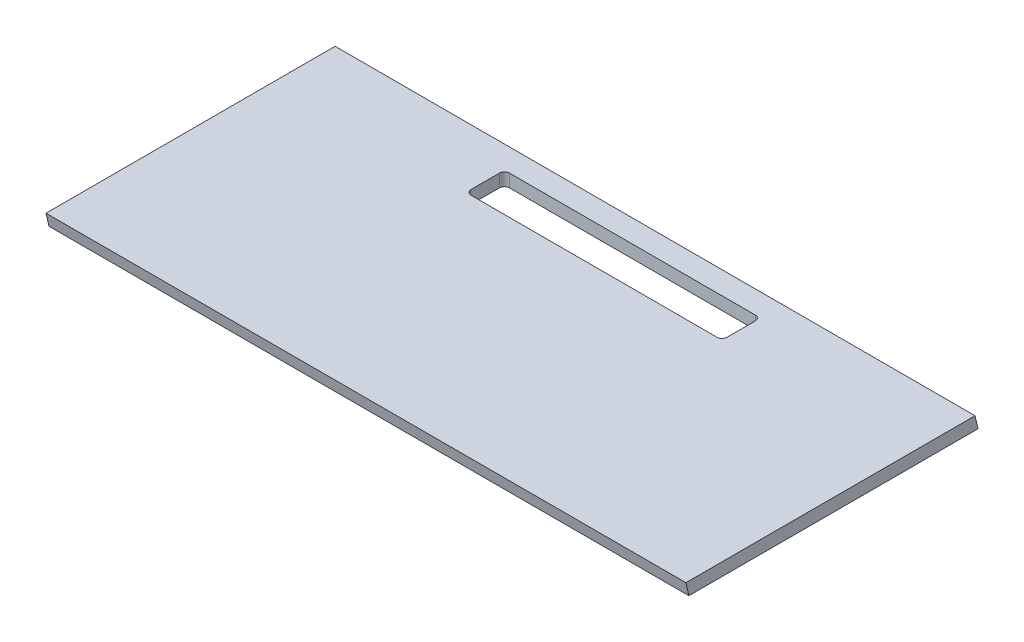
SolidWorks part; units mm, degrees
ref_plane "Ön Düzlem" through (0, 0, 0) normal (0, 0, 1) x (1, 0, 0)
ref_plane "Üst Düzlem" through (0, 0, 0) normal (0, 1, 0) x (1, 0, 0)
ref_plane "Sağ Düzlem" through (0, 0, 0) normal (1, 0, 0) x (0, 0, -1)
sketch "Sketch2" plane through (0, 0, 0) normal (0, 1, 0) x (1, 0, 0)
  line L1 (-250, -114.1) -> (250, -114.1)
  line L2 (-250, -114.1) -> (-250, 114.1)
  line L3 (-250, 114.1) -> (250, 114.1)
  line L4 (250, -114.1) -> (250, 114.1)
  line L5 (-250, -114.1) -> (250, 114.1) construction
  line L6 (-250, 114.1) -> (250, -114.1) construction
  point P0 (0, 0)
  dimension "D1" = 500
  dimension "D2" = 228.2
extrude "Boss-Extrude1" add sketch "Sketch2" along normal blind 10
sketch "Sketch3" plane through (0, 10, 0) normal (0, 1, 0) x (1, 0, 0)
  line L1 (-100, 94.1) -> (100, 94.1)
  line L2 (-100, 94.1) -> (-100, 64.1)
  line L3 (-100, 64.1) -> (100, 64.1)
  line L4 (100, 94.1) -> (100, 64.1)
  line L5 (-100, 94.1) -> (100, 64.1) construction
  line L6 (-100, 64.1) -> (100, 94.1) construction
  line L7 (250, 114.1) -> (-250, 114.1) construction
  point P0 (0, 0)
  dimension "D1" = 200
  dimension "D2" = 30
  dimension "D3" = 20
extrude "Cut-Extrude1" cut sketch "Sketch3" along direction (0, -1, 0) on the side against the normal up to next (10 mm away)
fillet "Fillet1" radius 4 4 edges at (100, 5, -94.1) (100, 5, -64.1) (-100, 5, -64.1) (-100, 5, -94.1)
sketch "Sketch4" plane through (250, 0, 0) normal (1, 0, 0) x (0, 0, -1)
  line L0 (114.1, 0) -> (111.7913, 10)
  line L1 (-114.1, 10) -> (114.1, 10) construction
  line L2 (111.7913, 10) -> (114.1, 10)
  line L3 (114.1, 10) -> (114.1, 0)
  line L4 (-114.1, 0) -> (-114.1, 10)
  line L5 (-114.1, 10) -> (-114.1, 0) construction
  line L6 (-114.1, 10) -> (-111.7913, 0)
  line L7 (-114.1, 0) -> (114.1, 0) construction
  line L9 (-111.7913, 0) -> (-114.1, 0)
  dimension "D1" = 13
  dimension "D2" = 13
extrude "Cut-Extrude2" cut sketch "Sketch4" against normal up to next
